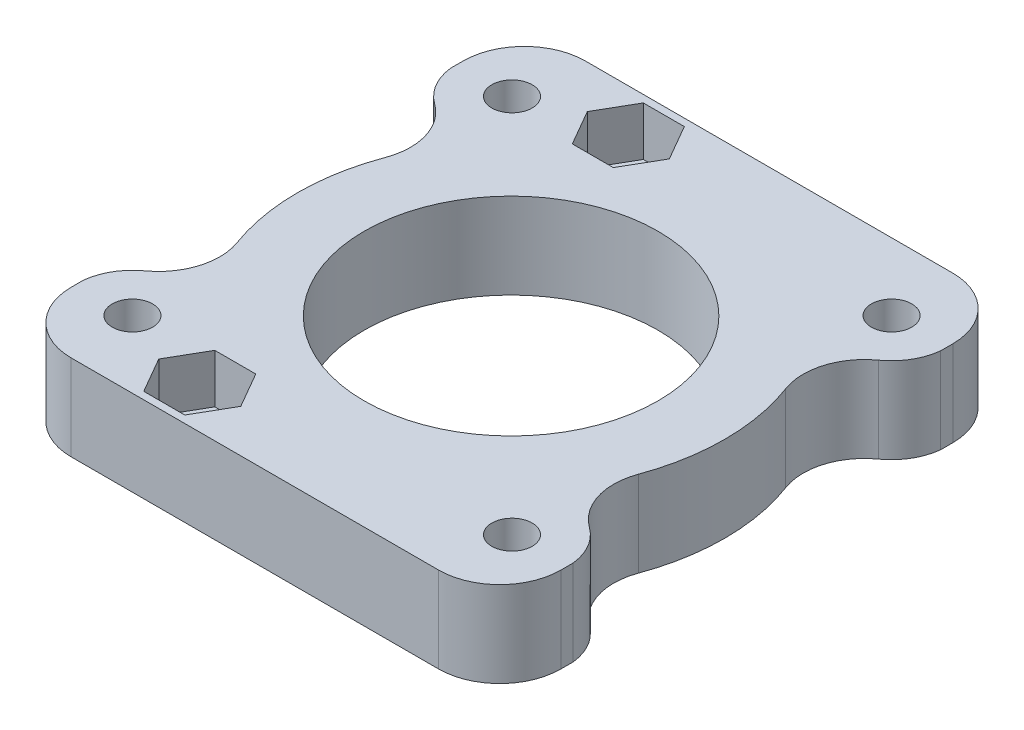
SolidWorks part; units mm, degrees
ref_plane "Спереди" through (0, 0, 0) normal (0, 0, 1) x (1, 0, 0)
ref_plane "Сверху" through (0, 0, 0) normal (0, 1, 0) x (1, 0, 0)
ref_plane "Справа" through (0, 0, 0) normal (1, 0, 0) x (0, 0, -1)
sketch "Эскиз1" plane through (0, 0, 0) normal (0, 1, 0) x (1, 0, 0)
  line L0 (-8, 17.5739) -> (-8, -17.4261) construction
  line L1 (-20, -14.9261) -> (-20, -15.9261)
  line L2 (15.5, 15.5739) -> (-15.5, 15.5739) construction
  line L3 (15.5, 15.5739) -> (15.5, -15.4261) construction
  line L4 (15.5, -15.4261) -> (-15.5, -15.4261) construction
  line L5 (-15.5, 15.5739) -> (-15.5, -15.4261) construction
  line L6 (15.5, 15.5739) -> (-15.5, -15.4261) construction
  line L7 (15.5, -15.4261) -> (-15.5, 15.5739) construction
  line L8 (15, 21.0739) -> (-15, 21.0739)
  line L9 (20, 16.0739) -> (20, 15.0739)
  line L10 (15, -20.9261) -> (-15, -20.9261)
  line L11 (-20, 16.0739) -> (-20, 15.0739)
  line L12 (20, 21.0739) -> (-20, -20.9261) construction
  line L13 (20, -20.9261) -> (-20, 21.0739) construction
  line L14 (20, -14.9261) -> (20, -15.9261)
  circle A0 centre (-8, -17.4261) radius 1.6
  circle A1 centre (-8, 17.5739) radius 1.6
  circle A2 centre (0, 0) radius 12
  circle A3 centre (-15.5, 15.5739) radius 1.65
  circle A4 centre (15.5, 15.5739) radius 1.65
  circle A5 centre (15.5, -15.4261) radius 1.65
  circle A6 centre (-15.5, -15.4261) radius 1.65
  arc A7 (-15, -20.9261) -> (-20, -15.9261) centre (-15, -15.9261) cw
  arc A8 (20, -15.9261) -> (15, -20.9261) centre (15, -15.9261) cw
  arc A9 (15, 21.0739) -> (20, 16.0739) centre (15, 16.0739) cw
  arc A10 (-15, 21.0739) -> (-20, 16.0739) centre (-15, 16.0739) ccw
  arc A11 (-18.2137, 19.1983) -> (-18.1318, 11.8897) centre (-15.5, 15.5739) ccw
  arc A12 (-18.1523, -11.7565) -> (-16.3851, -5.988) centre (-21.0813, -7.7043) ccw
  arc A13 (20, -15.9261) -> (18.1523, -11.7565) centre (15.5, -15.4261) ccw
  arc A14 (18.1318, 11.8897) -> (20, 16.0739) centre (15.5, 15.5739) ccw
  arc A15 (-16.3516, 6.0789) -> (-18.1318, 11.8897) centre (-21.0382, 7.8212) ccw
  arc A16 (16.3851, -5.988) -> (16.3516, 6.0789) centre (0, 0) ccw
  arc A17 (-18.1523, -11.7565) -> (-20, -15.9261) centre (-15.5, -15.4261) ccw
  arc A18 (-16.3516, 6.0789) -> (-16.3851, -5.988) centre (0, 0) ccw
  arc A19 (18.1523, -11.7565) -> (16.3851, -5.988) centre (21.0813, -7.7043) cw
  arc A20 (16.3516, 6.0789) -> (18.1318, 11.8897) centre (21.0382, 7.8212) cw
  dimension "D1" = 24
  dimension "D2" = 3.2
  dimension "D3" = 3.2
  dimension "D8" = 40
  dimension "D9" = 3.3
  dimension "D10" = 3.3
  dimension "D11" = 3.3
  dimension "D12" = 3.3
  dimension "D13" = 5
  dimension "D14" = 5
  dimension "D15" = 5
  dimension "D16" = 5
  dimension "D17" = 5
  dimension "D4" = 35
  dimension "D5" = 31
  dimension "D6" = 31
  dimension "D7" = 42
extrude "Бобышка-Вытянуть2" add sketch "Эскиз1" along normal blind 7
sketch "Эскиз2" plane through (0, 7, 0) normal (0, 1, 0) x (1, 0, 0)
  line L1 (-11.3486, 17.5739) -> (-9.6743, 14.6739)
  line L2 (-9.6743, 14.6739) -> (-6.3257, 14.6739)
  line L3 (-6.3257, 14.6739) -> (-4.6514, 17.5739)
  line L4 (-4.6514, 17.5739) -> (-6.3257, 20.4739)
  line L5 (-6.3257, 20.4739) -> (-9.6743, 20.4739)
  line L6 (-9.6743, 20.4739) -> (-11.3486, 17.5739)
  line L7 (-4.6514, -17.4261) -> (-6.3257, -14.5261)
  line L8 (-6.3257, -14.5261) -> (-9.6743, -14.5261)
  line L9 (-9.6743, -14.5261) -> (-11.3486, -17.4261)
  line L10 (-11.3486, -17.4261) -> (-9.6743, -20.3261)
  line L11 (-9.6743, -20.3261) -> (-6.3257, -20.3261)
  line L12 (-6.3257, -20.3261) -> (-4.6514, -17.4261)
  circle A0 centre (-8, 17.5739) radius 2.9 construction
  circle A1 centre (-8, -17.4261) radius 2.9 construction
  dimension "D1" = 5.8
extrude "Вырез-Вытянуть1" cut sketch "Эскиз2" against normal blind 4
chamfer "Фаска1" distance 1.5 angle 45 4 edges at (15.5, 0, -13.9239) (-15.5, 0, -13.9239) (-15.5, 0, 17.0761) (15.5, 0, 17.0761)
